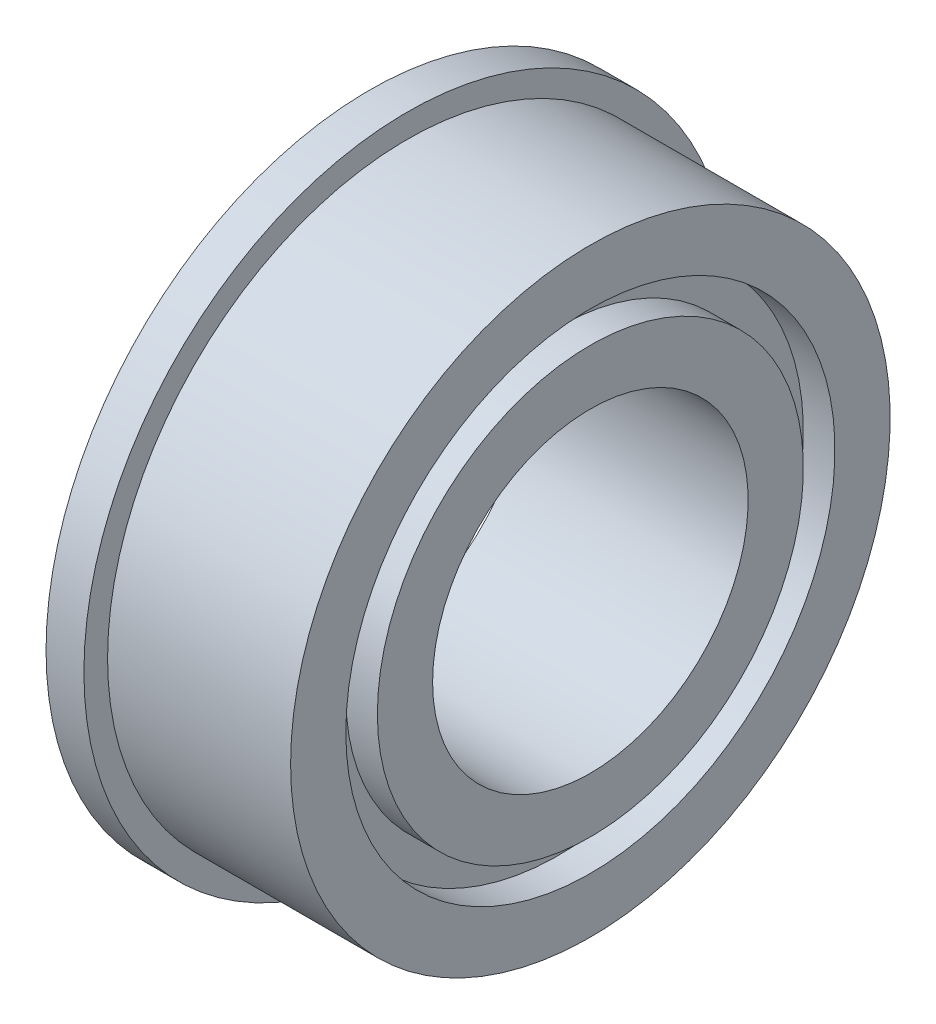
SolidWorks part; units mm, degrees
material "AISI 304"
ref_plane "Front Plane" through (0, 0, 0) normal (0, 0, 1) x (1, 0, 0)
ref_plane "Top Plane" through (0, 0, 0) normal (0, 1, 0) x (1, 0, 0)
ref_plane "Right Plane" through (0, 0, 0) normal (1, 0, 0) x (0, 0, -1)
sketch "Sketch2" plane through (0, 0, 0) normal (0, 0, 1) x (1, 0, 0)
  line L0 (0, 0) -> (12.0838, 0) construction
  line L1 (-1.2, 10.25) -> (0, 10.25)
  line L2 (-1.2, 10.25) -> (-1.2, 7.75)
  line L3 (-1.2, 5) -> (5.8, 5)
  line L4 (5.8, 9.5) -> (5.8, 7.75)
  line L5 (-1.2, 6.75) -> (-1.2, 5)
  line L6 (0, 10.25) -> (0, 9.5)
  line L7 (0, 9.5) -> (5.8, 9.5)
  line L8 (5.8, 6.75) -> (5.8, 5)
  line L9 (-1.2, 6.75) -> (-0.2, 6.75)
  line L10 (0, 9.5) -> (0, 0) construction
  line L11 (-1.2, 7.75) -> (-0.2, 7.75)
  line L12 (-0.2, 6.75) -> (-0.2, 7.75)
  line L13 (5.8, 7.75) -> (4.8, 7.75)
  line L15 (5.8, 6.75) -> (4.8, 6.75)
  line L16 (4.8, 7.75) -> (4.8, 6.75)
  dimension "D1" = 10
  dimension "D2" = 19
  dimension "D3" = 1
  dimension "D4" = 7
  dimension "D5" = 1.2
  dimension "D6" = 20.5
  dimension "D7" = 1
revolve "Revolve1" add sketch "Sketch2" angle 360 about L0
